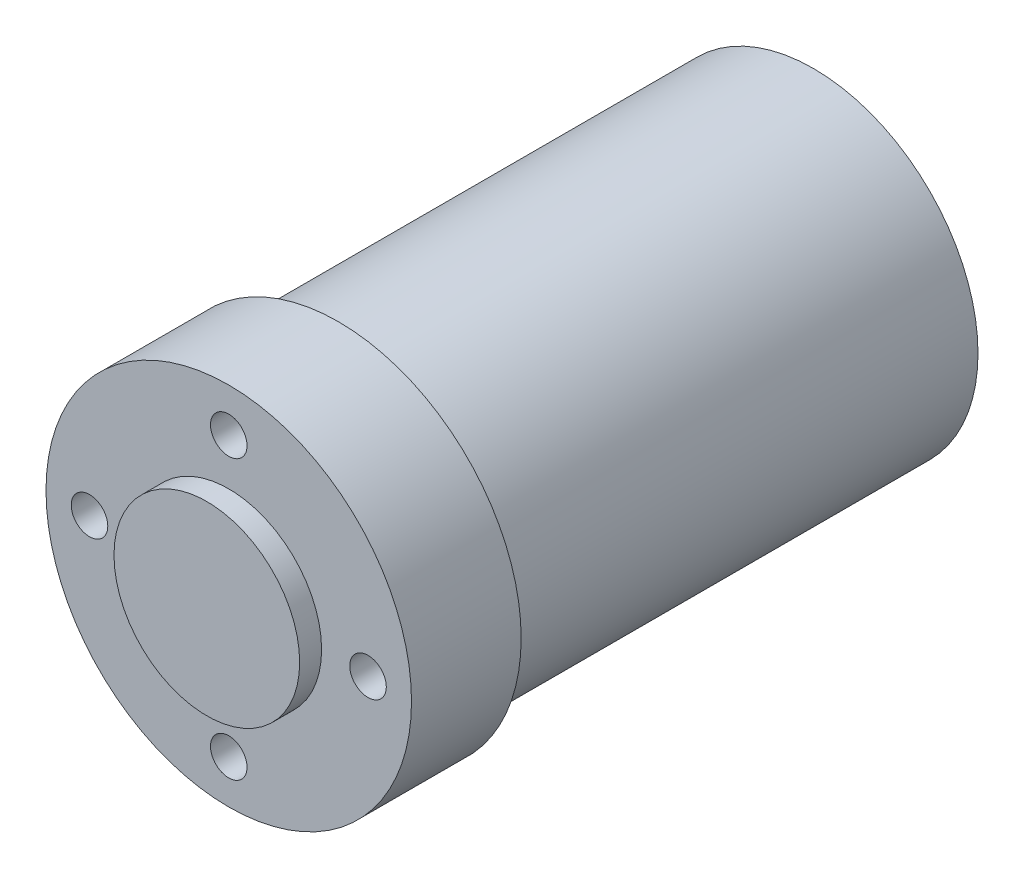
SolidWorks part; units mm, degrees
ref_plane "Front Plane" through (0, 0, 0) normal (0, 0, 1) x (1, 0, 0)
ref_plane "Top Plane" through (0, 0, 0) normal (0, 1, 0) x (1, 0, 0)
ref_plane "Right Plane" through (0, 0, 0) normal (1, 0, 0) x (0, 0, -1)
ref_plane "Plane1" through (0, 0, 0) normal (0, -1, 0) x (1, 0, 0)
sketch "Sketch1" plane through (0, 0, 0) normal (0, -1, 0) x (1, 0, 0)
  line L0 (25, 80) -> (0, 80)
  line L1 (0, 80) -> (0, 65)
  line L2 (0, 65) -> (25, 65)
  line L3 (25, 65) -> (25, 80)
  line L4 (0, 80) -> (0, 65) construction
revolve "Revolve1" add sketch "Sketch1" angle 360 about L4
sketch "Sketch2" plane through (0, 0, 80) normal (0, 0, 1) x (1, 0, 0)
  circle A0 centre (0, 0) radius 12.7
extrude "Boss-Extrude1" add sketch "Sketch2" along normal blind 3
sketch "Sketch3" plane through (0, 0, 65) normal (0, 0, -1) x (-1, 0, 0)
  circle A0 centre (0, 0) radius 22.4917
extrude "Boss-Extrude2" add sketch "Sketch3" along normal blind 65
hole_wizard "#10 Clearance Hole1" positions "Sketch5" profile "Sketch4" hole size "#10" standard "ANSI Inch"
sketch "Sketch5" plane through (0, 0, 0) normal (0, 0, -1) x (-1, 0, 0)
  point P0 (-12.3744, 12.3744)
  point P1 (-17.5, 0)
  point P2 (-12.3744, -12.3744)
  point P3 (0, -17.5)
  point P4 (12.3744, -12.3744)
  point P5 (17.5, 0)
  point P6 (12.3744, 12.3744)
  point P7 (0, 17.5)
sketch "Sketch4" plane through (12.3744, 12.3744, 0) normal (1, 0, 0) x (0, 1, 0)
  line L0 (0, 0) -> (0, 8)
  line L1 (0, 8) -> (2.5, 8)
  line L2 (2.5, 8) -> (2.5, 0)
  line L5 (2.5, 0) -> (0, 0)
  line L10 (0, 8) -> (-2.5, 8) construction
  line L11 (0, -6.35) -> (0, 107.95) construction
  dimension "Hole Dia." = 5
  dimension "Hole Depth" = 8
  dimension "Drill Angle" = 180
hole_wizard "#10 Clearance Hole2" positions "Sketch7" profile "Sketch6" hole size "#10" standard "ANSI Inch"
sketch "Sketch7" plane through (0, 0, 80) normal (0, 0, 1) x (1, 0, 0)
  point P0 (-19.05, 0)
  point P1 (0, -19.05)
  point P2 (19.05, 0)
  point P3 (0, 19.05)
sketch "Sketch6" plane through (-19.05, 0, 80) normal (1, 0, 0) x (0, -1, 0)
  line L0 (0, 0) -> (0, 12.446)
  line L1 (0, 12.446) -> (2.5, 12.446)
  line L2 (2.5, 12.446) -> (2.5, 0)
  line L5 (2.5, 0) -> (0, 0)
  line L10 (0, 12.446) -> (-2.5, 12.446) construction
  line L11 (0, -6.35) -> (0, 107.95) construction
  dimension "Hole Dia." = 5
  dimension "Hole Depth" = 12.446
  dimension "Drill Angle" = 180
